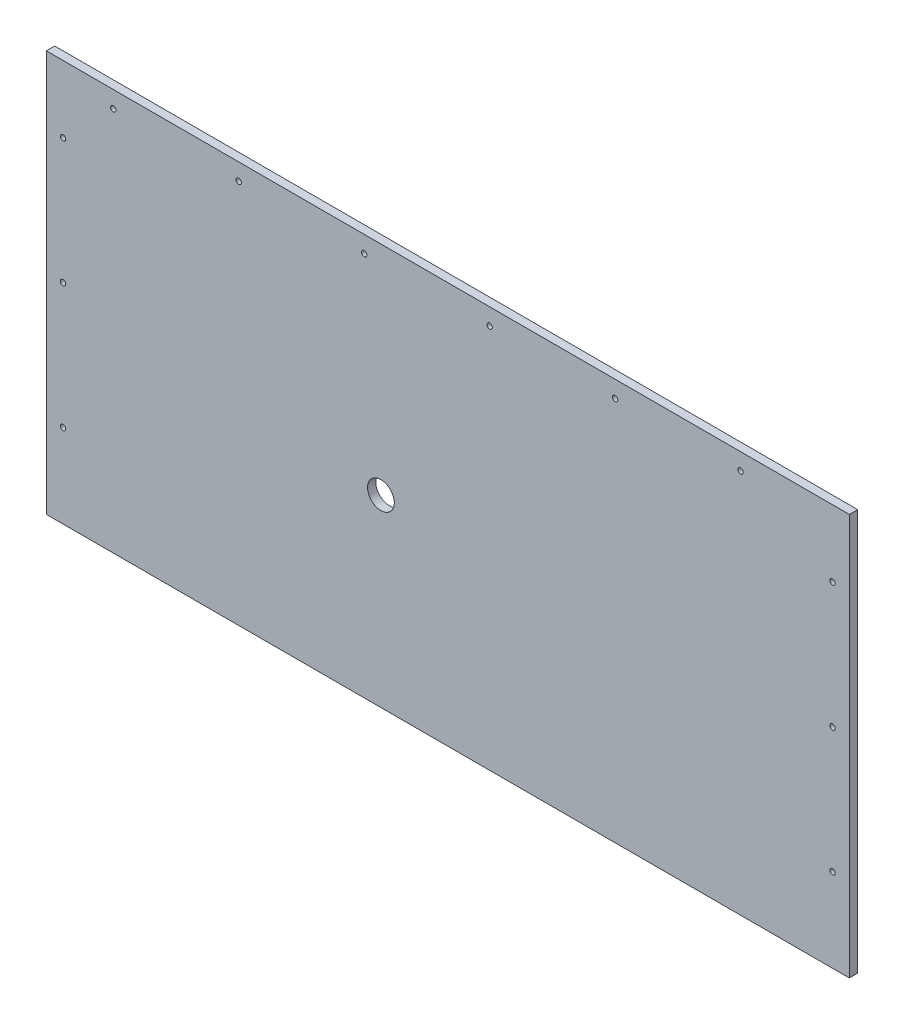
SolidWorks part; units mm, degrees
ref_plane "Front Plane" through (0, 0, 0) normal (0, 0, 1) x (1, 0, 0)
ref_plane "Top Plane" through (0, 0, 0) normal (0, 1, 0) x (1, 0, 0)
ref_plane "Right Plane" through (0, 0, 0) normal (1, 0, 0) x (0, 0, -1)
sketch "Sketch1" plane through (0, 0, 0) normal (0, 0, 1) x (1, 0, 0)
  line L1 (0, 0) -> (609.6, 0)
  line L2 (0, 0) -> (0, 304.8)
  line L3 (0, 304.8) -> (609.6, 304.8)
  line L4 (609.6, 0) -> (609.6, 304.8)
  dimension "D1" = 304.8
  dimension "D2" = 609.6
extrude "Boss-Extrude1" add sketch "Sketch1" along normal blind 6.35 contours L2 L3 L4 L1
sketch "Sketch2" plane through (0, 0, 6.35) normal (0, 0, 1) x (1, 0, 0)
  line L0 (0, 0) -> (0, 304.8) construction
  line L1 (0, 304.8) -> (609.6, 304.8) construction
  line L2 (304.8, 304.8) -> (304.8, 0) construction
  line L3 (0, 0) -> (609.6, 0) construction
  circle A0 centre (12.7, 254) radius 2.032
  circle A3 centre (12.7, 158.75) radius 2.032
  circle A4 centre (12.7, 63.5) radius 2.032
  circle A5 centre (596.9, 63.5) radius 2.032
  circle A6 centre (596.9, 158.75) radius 2.032
  circle A7 centre (596.9, 254) radius 2.032
  dimension "D3" = 4.064
  dimension "D4" = 3
  dimension "D1" = 12.7
  dimension "D2" = 50.8
extrude "Cut-Extrude4" cut sketch "Sketch2" against normal through all contours A0 | A3 | A4 | A5 | A6 | A7
sketch "Sketch4" plane through (0, 0, 6.35) normal (0, 0, 1) x (1, 0, 0)
  line L0 (0, 304.8) -> (609.6, 304.8) construction
  line L1 (0, 0) -> (0, 304.8) construction
  circle A0 centre (50.8, 292.1) radius 2.032
  circle A1 centre (146.05, 292.1) radius 2.032
  circle A2 centre (241.3, 292.1) radius 2.032
  circle A3 centre (336.55, 292.1) radius 2.032
  circle A4 centre (431.8, 292.1) radius 2.032
  circle A5 centre (527.05, 292.1) radius 2.032
  dimension "D1" = 4.064
  dimension "D2" = 12.7
  dimension "D3" = 50.8
  dimension "D4" = 95.25
extrude "Cut-Extrude7" cut sketch "Sketch4" against normal through all
sketch "Sketch5" plane through (0, 0, 0) normal (0, 0, -1) x (-1, 0, 0)
  line L0 (0, 0) -> (0, 304.8) construction
  line L1 (0, 304.8) -> (-609.6, 304.8) construction
  circle A0 centre (-254, 139.7) radius 10.16
  dimension "D1" = 20.32
  dimension "D2" = 254
  dimension "D3" = 165.1
extrude "Cut-Extrude8" cut sketch "Sketch5" against normal through all
